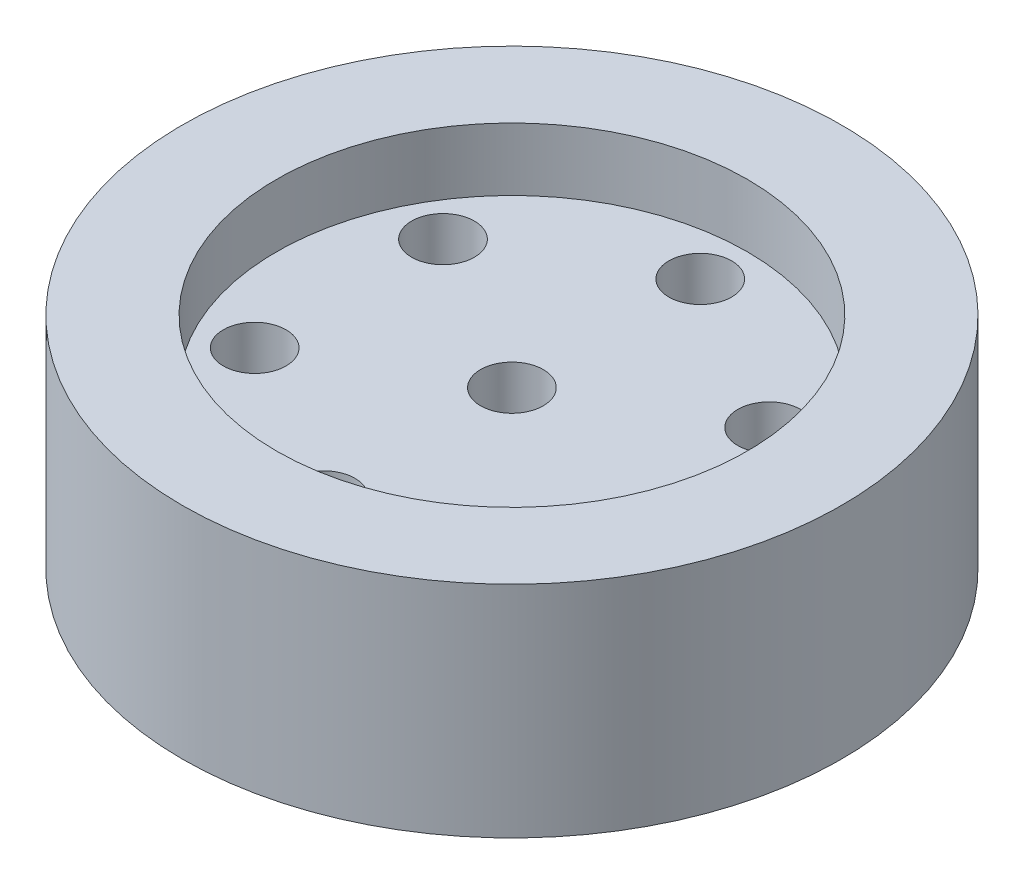
SolidWorks part; units mm, degrees
ref_plane "Front Plane" through (0, 0, 0) normal (0, 0, 1) x (1, 0, 0)
ref_plane "Top Plane" through (0, 0, 0) normal (0, 1, 0) x (1, 0, 0)
ref_plane "Right Plane" through (0, 0, 0) normal (1, 0, 0) x (0, 0, -1)
sketch "Sketch1" plane through (0, 0, 0) normal (0, 1, 0) x (1, 0, 0)
  circle A0 centre (0, 0) radius 21
  dimension "D1" = 42
extrude "Boss-Extrude1" add sketch "Sketch1" along normal blind 14
sketch "Sketch2" plane through (0, 14, 0) normal (0, 1, 0) x (1, 0, 0)
  circle A0 centre (0, 0) radius 15
  dimension "D1" = 30
extrude "Cut-Extrude1" cut sketch "Sketch2" against normal blind 4
sketch "Sketch3" plane through (0, 0, 0) normal (0, -1, 0) x (1, 0, 0)
  circle A0 centre (0, 0) radius 19
  circle A1 centre (0, 0) radius 5
  dimension "D1" = 38
  dimension "D2" = 10
extrude "Cut-Extrude2" cut sketch "Sketch3" against normal blind 4
sketch "Sketch4" plane through (0, 0, 0) normal (0, -1, 0) x (1, 0, 0)
  circle A0 centre (0, 0) radius 2
  dimension "D1" = 4
extrude "Cut-Extrude3" cut sketch "Sketch4" against normal through all
sketch "Sketch5" plane through (0, 4, 0) normal (0, -1, 0) x (1, 0, 0)
  circle A0 centre (0, 0) radius 12 construction
  circle A1 centre (0, 12) radius 2
  circle A2 centre (10.3923, 6) radius 2
  circle A3 centre (10.3923, -6) radius 2
  circle A4 centre (0, -12) radius 2
  circle A5 centre (-10.3923, -6) radius 2
  circle A6 centre (-10.3923, 6) radius 2
  dimension "D1" = 24
  dimension "D2" = 4
  dimension "D3" = 6
extrude "Cut-Extrude4" cut sketch "Sketch5" against normal through all
